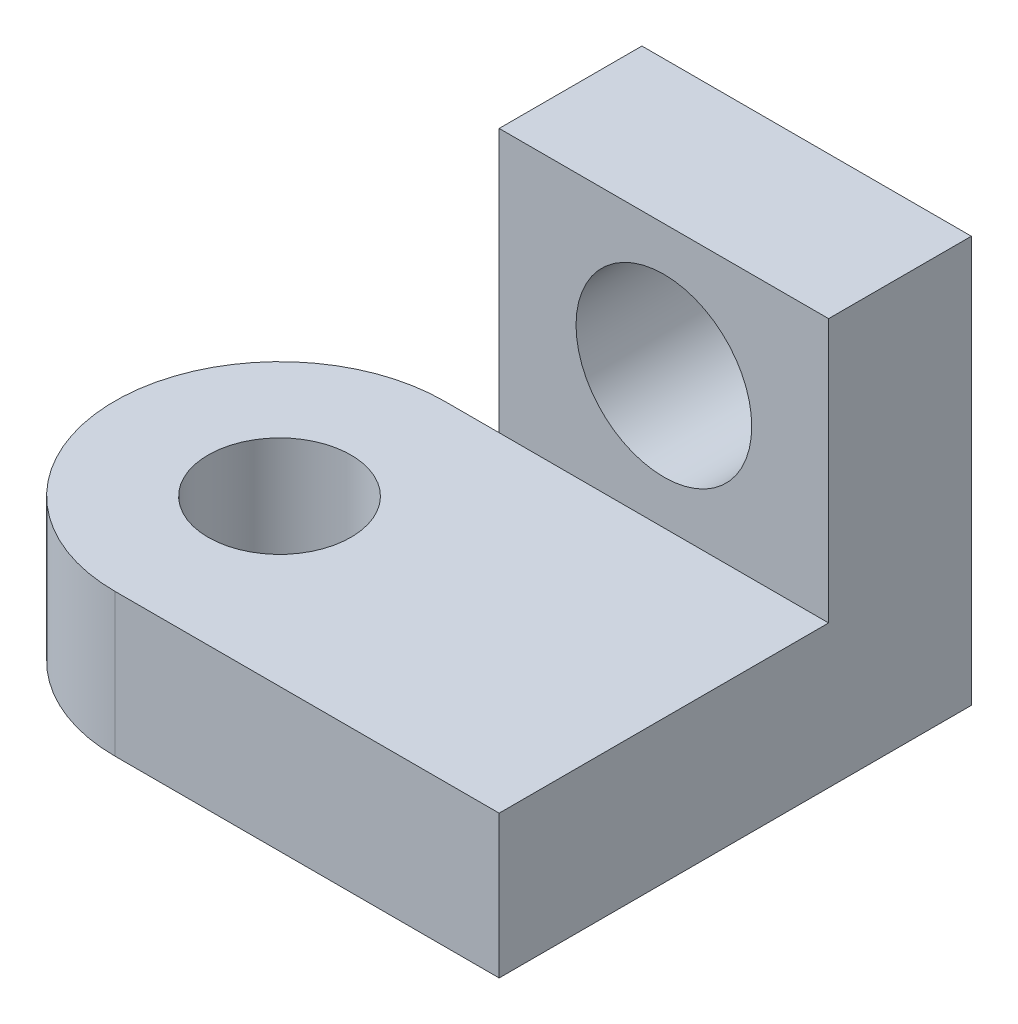
SolidWorks part; units mm, degrees
ref_plane "Front Plane" through (0, 0, 0) normal (0, 0, 1) x (1, 0, 0)
ref_plane "Top Plane" through (0, 0, 0) normal (0, 1, 0) x (1, 0, 0)
ref_plane "Right Plane" through (0, 0, 0) normal (1, 0, 0) x (0, 0, -1)
sketch "Sketch1" plane through (0, 0, 0) normal (0, 1, 0) x (1, 0, 0)
  line L0 (0, 0) -> (-35, 0)
  line L1 (0, 0) -> (0, 30)
  line L2 (0, 30) -> (-35, 30)
  arc A0 (-35, 30) -> (-35, 0) centre (-35, 15) ccw
  circle A1 centre (-35, 15) radius 6.5
  dimension "D3" = 15
  dimension "D5" = 13
  dimension "D1" = 35
  dimension "D2" = 30
  dimension "D4" = 35
extrude "Boss-Extrude1" add sketch "Sketch1" along normal blind 13 contours A1 | A0 L0 L1 L2
sketch "Sketch2" plane through (0, 0, 0) normal (0, 1, 0) x (1, 0, 0)
  line L1 (0, 30) -> (-30, 30)
  line L2 (0, 30) -> (0, 43)
  line L3 (0, 43) -> (-30, 43)
  line L4 (-30, 30) -> (-30, 43)
  dimension "D1" = 30
  dimension "D2" = 13
extrude "Boss-Extrude2" add sketch "Sketch2" along normal blind 37 contours L4 L3 L2 L1
sketch "Sketch3" plane through (0, 0, 0) normal (0, 0, 1) x (1, 0, 0)
  line L0 (-30, 37) -> (-30, 13) construction
  line L1 (0, 13) -> (-35, 13) construction
  circle A0 centre (-15, 25) radius 8
  point P6 (-15.3859, 19.9222)
  dimension "D1" = 16
  dimension "D2" = 15
  dimension "D3" = 12
extrude "Cut-Extrude1" cut sketch "Sketch3" against normal blind 43 contours A0
